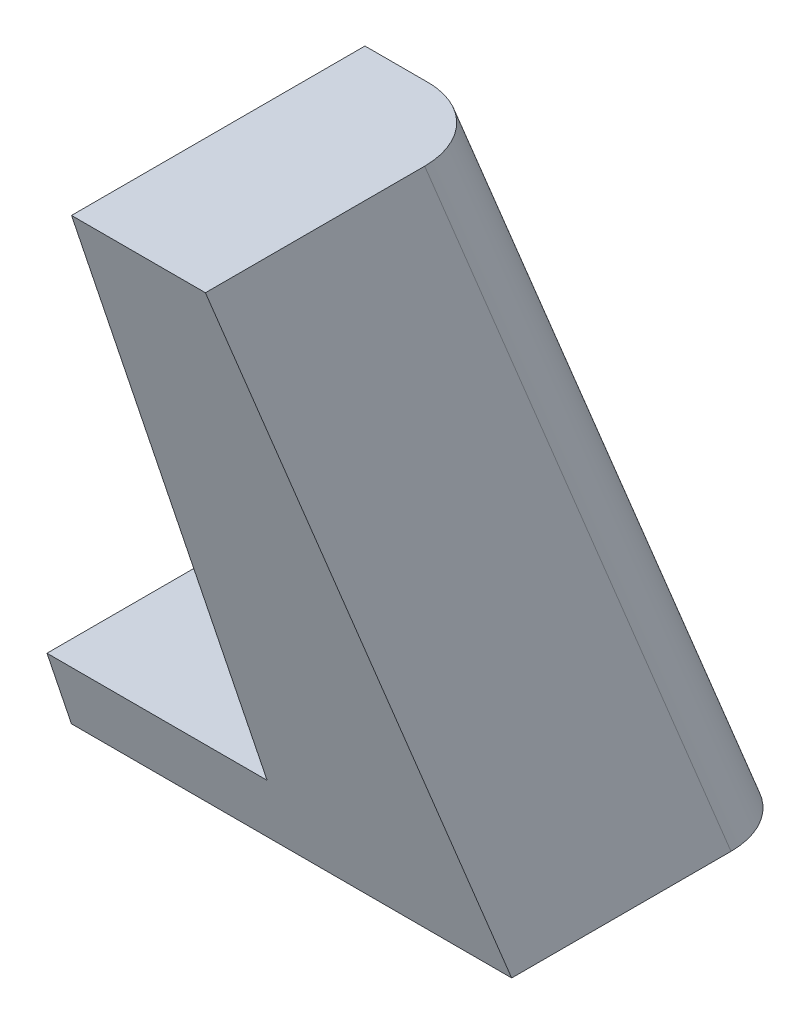
SolidWorks part; units mm, degrees
ref_plane "Спереди" through (0, 0, 0) normal (0, 0, 1) x (1, 0, 0)
ref_plane "Сверху" through (0, 0, 0) normal (0, 1, 0) x (1, 0, 0)
ref_plane "Справа" through (0, 0, 0) normal (1, 0, 0) x (0, 0, -1)
sketch "Эскиз1" plane through (0, 0, 0) normal (0, 1, 0) x (1, 0, 0)
  line L1 (-82.6594, 0) -> (83.4888, 0) construction
  line L3 (-45, 0) -> (-45, 45)
  line L4 (-45, 45) -> (45, 45)
  line L5 (45, 45) -> (45, -45)
  line L6 (45, -45) -> (-45, -45)
  line L7 (-45, -45) -> (-45, 0)
  dimension "D1" = 90
  dimension "D2" = 90
  dimension "D4" = 45
sketch "Эскиз2" plane through (0, 0, 0) normal (0, 0, 1) x (1, 0, 0)
  line L0 (-45, 0) -> (-30, 0)
  line L1 (-30, 0) -> (-30, 45)
  line L2 (45, 0) -> (-45, 0) construction
  line L3 (39.125, 45) -> (45, 0)
  line L4 (-45, 0) -> (-30, 0)
  line L5 (0, 0) -> (0, 57.5371) construction
  line L6 (-39.125, 45) -> (-30, 45)
  line L7 (39.125, 45) -> (-39.125, 45)
  line L8 (-39.125, 45) -> (-45, 0)
  line L9 (39.125, 45) -> (30, 45)
  line L10 (45, 0) -> (30, 0)
  line L11 (30, 0) -> (30, 45)
  line L12 (45, 0) -> (30, 0)
  point P4 (0, 45)
  dimension "D1" = 45
  dimension "D2" = 39.125
  dimension "D3" = 82.562
  dimension "D4" = 15
  dimension "D5" = 45
sketch "Эскиз4" plane through (0, 0, 0) normal (1, 0, 0) x (0, 0, -1)
  line L0 (-50.289, 0) -> (-50, 45)
  line L1 (-35.289, 45) -> (-50, 45)
  line L2 (0, 0) -> (30.289, 0)
  line L3 (-15.2933, 45) -> (-35.289, 45)
  line L4 (-50.289, 0) -> (-35.289, 45)
  line L5 (-50.289, 0) -> (-30.289, 0)
  line L6 (-30.289, 0) -> (-15.2933, 45)
  line L7 (-15.2933, 45) -> (15.2933, 45)
  line L8 (0, 45) -> (0, 0)
  line L9 (0, 0) -> (-30.289, 0)
  line L10 (30.289, 0) -> (15.2933, 45)
  line L11 (50.289, 0) -> (30.289, 0)
  line L12 (50.289, 0) -> (35.289, 45)
  line L13 (15.2933, 45) -> (35.289, 45)
  line L14 (35.289, 45) -> (50, 45)
  line L15 (50.289, 0) -> (50, 45)
  line L16 (0, 45) -> (15.2933, 45)
  dimension "D1" = 71.565
  dimension "D2" = 71.57
  dimension "D3" = 19.9957
  dimension "D4" = 45
  dimension "D5" = 20
  dimension "D6" = 50
  dimension "D7" = 30.289
  dimension "D8" = 45
extrude "Бобышка-Вытянуть6" add sketch "Эскиз2" against normal blind 50 contours L11 L10 L3 L7
extrude "Вырез-Вытянуть5" cut sketch "Эскиз4" along normal blind 63 contours L12 L15 L14 | L2 L10 L7 L8
sketch "Эскиз7" plane through (30, 0, 0) normal (-1, 0, 0) x (0, 0, 1)
  line L0 (-50, 0) -> (-50, 0.8669)
  line L1 (-35.289, 45) -> (-50, 0.8669) construction
  line L2 (-50, 0) -> (-50, 0.8669) construction
  line L4 (-50, 0.8669) -> (-48.6223, 5)
  line L5 (-15.2933, 45) -> (-30.289, 0) construction
  line L6 (-28.6228, 5) -> (-30.289, 0)
  line L7 (-30.289, 0) -> (-50, 0)
  line L10 (-48.6223, 5) -> (-28.6228, 5)
  dimension "D1" = 19.9995
extrude "Бобышка-Вытянуть7" add sketch "Эскиз7" along normal blind 15
fillet "Скругление2" radius 5 2 edges at (44.9434, 0.4335, -50) (42.0059, 22.9335, -42.6445)
sketch "Эскиз8" plane through (0, 5, 0) normal (0, 1, 0) x (1, 0, 0)
  line L0 (15, 38.6225) -> (30, 38.6225) construction
  line L1 (15, 28.6228) -> (15, 48.6223) construction
  line L2 (30, 48.6223) -> (30, 28.6228) construction
  line L3 (22.5, 48.6223) -> (22.5, 28.6228) construction
  line L4 (15, 48.6223) -> (30, 48.6223) construction
  line L5 (15, 28.6228) -> (30, 28.6228) construction
  circle A0 centre (22.5, 38.6225) radius 2.5
  dimension "D1" = 5
extrude "Вырез-Вытянуть6" cut sketch "Эскиз8" against normal blind 10
